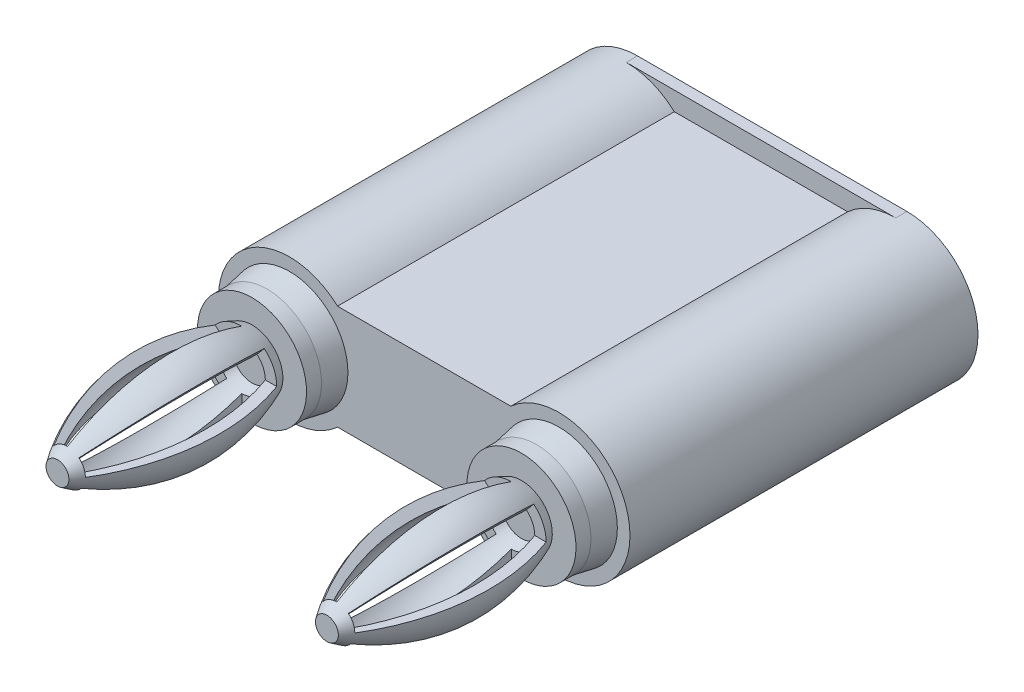
SolidWorks part; units mm, degrees
ref_plane "Front Plane" through (0, 0, 0) normal (0, 0, 1) x (1, 0, 0)
ref_plane "Top Plane" through (0, 0, 0) normal (0, 1, 0) x (1, 0, 0)
ref_plane "Right Plane" through (0, 0, 0) normal (1, 0, 0) x (0, 0, -1)
sketch "Sketch1" plane through (0, 0, 0) normal (0, 0, 1) x (1, 0, 0)
  line L0 (0, 4.826) -> (27.94, 4.826) construction
  line L1 (4.826, 0) -> (23.114, 0)
  line L3 (4.826, 9.652) -> (23.114, 9.652)
  arc A2 (4.826, 9.652) -> (4.826, 0) centre (4.826, 4.826) ccw
  arc A3 (23.114, 0) -> (23.114, 9.652) centre (23.114, 4.826) ccw
  dimension "D3" = 4.826
  dimension "D4" = 4.826
  dimension "D2" = 18.288
  dimension "D1" = 9.652
extrude "Boss-Extrude1" add sketch "Sketch1" against normal blind 0.762
sketch "Sketch2" plane through (0, 0, 0) normal (0, 0, 1) x (1, 0, 0)
  line L0 (23.114, 9.652) -> (4.826, 9.652) construction
  line L1 (8.0887, 8.382) -> (19.8513, 8.382)
  line L2 (4.826, 0) -> (23.114, 0) construction
  line L3 (8.0887, 1.27) -> (19.8513, 1.27)
  arc A0 (8.0887, 8.382) -> (8.0887, 1.27) centre (4.826, 4.826) ccw
  arc A1 (19.8513, 1.27) -> (19.8513, 8.382) centre (23.114, 4.826) ccw
  dimension "D3" = 4.826
  dimension "D4" = 4.826
  dimension "D1" = 1.27
  dimension "D2" = 1.27
extrude "Boss-Extrude2" add sketch "Sketch2" along normal blind 22.86
sketch "Sketch3" plane through (0, 0, 22.86) normal (0, 0, 1) x (1, 0, 0)
  circle A0 centre (4.826, 4.826) radius 3.9688
  circle A1 centre (23.114, 4.826) radius 3.9688
  dimension "D1" = 7.9375
extrude "Boss-Extrude3" add sketch "Sketch3" along normal blind 1.524 draft 10
ref_plane "Plane1" through (4.826, 0, 0) normal (1, 0, 0) x (0, 0, -1)
sketch "Sketch4" plane through (4.826, 0, 0) normal (1, 0, 0) x (0, 0, -1)
  line L0 (0.762, 4.826) -> (-24.384, 4.826) construction
  line L1 (0.762, 0) -> (0.762, 9.652) construction
  line L2 (-24.384, 8.526) -> (-24.384, 1.126) construction
  line L3 (-24.384, 4.826) -> (-38.608, 4.826) construction
  line L4 (-24.384, 4.826) -> (-24.384, 1.126)
  line L5 (-24.384, 1.126) -> (-25.4, 1.126)
  line L6 (-25.4, 1.126) -> (-25.4, 2.7327)
  line L7 (-24.384, 4.826) -> (-38.608, 4.826)
  line L8 (-38.608, 4.0484) -> (-38.608, 4.826)
  arc A0 (-25.4, 2.7327) -> (-38.608, 4.0484) centre (-30.8186, 15.2907) cw
  dimension "D1" = 39.37
  dimension "D2" = 1.016
revolve "Revolve1" add sketch "Sketch4" angle 360 about L7
sketch "Sketch6" plane through (4.826, 0, 0) normal (1, 0, 0) x (0, 0, -1)
  line L0 (-25.4, 4.826) -> (-38.608, 4.826) construction
  line L1 (-25.4, 8.526) -> (-25.4, 1.126) construction
  line L2 (-38.608, 5.6036) -> (-38.608, 4.0484) construction
  line L3 (-38.1629, 4.826) -> (-38.1629, 4.2318)
  line L4 (-25.4, 4.826) -> (-25.4, 3.5037)
  line L5 (-25.4, 4.826) -> (-38.1629, 4.826)
  arc A0 (-25.4, 3.5037) -> (-38.1629, 4.2318) centre (-31.0436, 16.8012) cw
revolve "Cut-Revolve2" cut sketch "Sketch6" angle 360 about L0
sketch "Sketch7" plane through (4.826, 0, 0) normal (1, 0, 0) x (0, 0, -1)
  line L0 (-25.4, 4.826) -> (-38.608, 4.826) construction
  line L1 (-25.4, 6.9193) -> (-25.4, 2.7327) construction
  line L2 (-38.608, 5.6036) -> (-38.608, 4.0484) construction
  line L3 (-26.0928, 4.826) -> (-26.0928, 1.3516)
  line L4 (-26.0928, 1.3516) -> (-37.9299, 1.5767)
  line L5 (-37.9299, 1.5767) -> (-37.9299, 4.826)
  line L6 (-26.0928, 4.826) -> (-37.9299, 4.826)
revolve "Cut-Revolve3" cut sketch "Sketch7" angle 50 about L0
pattern_circular "CirPattern1" count 4 over 360 about axis through (4.826, 4.826, 38.608) along (0, 0, -1) of "Cut-Revolve3"
ref_plane "Plane2" through (13.97, 0, 0) normal (1, 0, 0) x (0, 0, -1)
pattern_linear "LPattern1" count 2 spacing 18.288 along (1, 0, 0) of "Cut-Revolve2", "Cut-Revolve3", "CirPattern1", "Revolve1"
